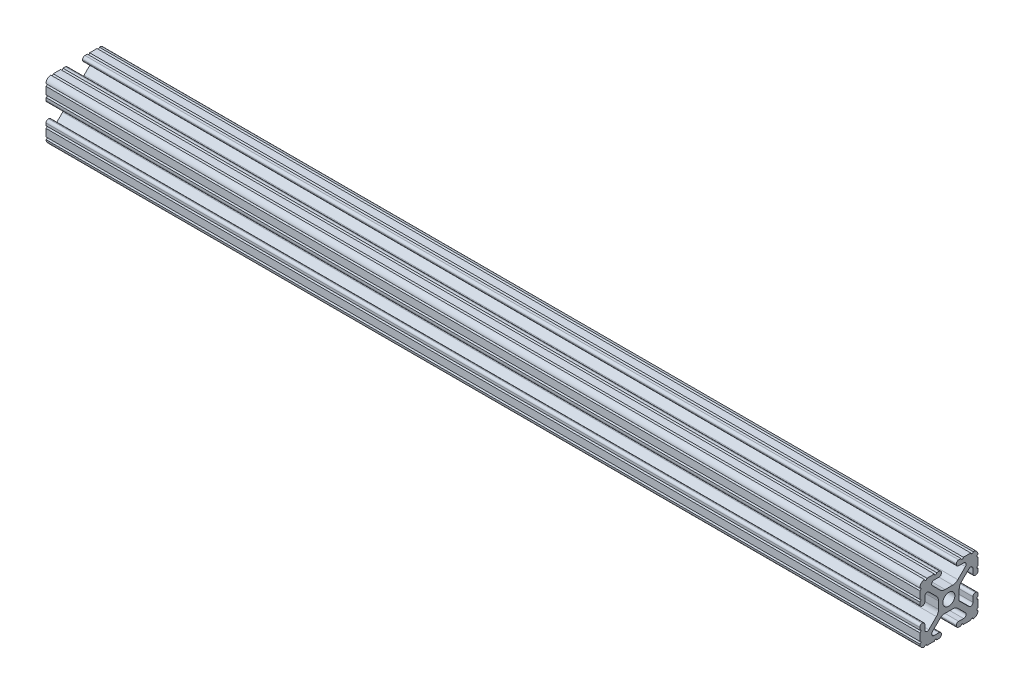
SolidWorks part; units mm, degrees
material "6061-T6 (SS)"
ref_plane "Front Plane" through (0, 0, 0) normal (0, 0, 1) x (1, 0, 0)
ref_plane "Top Plane" through (0, 0, 0) normal (0, 1, 0) x (1, 0, 0)
ref_plane "Right Plane" through (0, 0, 0) normal (1, 0, 0) x (0, 0, -1)
sketch "Sketch1" plane through (0, 0, 0) normal (1, 0, 0) x (0, 0, -1)
  line L0 (6.3331, -12.7) -> (9.5504, -12.7)
  line L1 (12.7, -9.5504) -> (12.7, -6.3331)
  line L2 (12.7, -5.3171) -> (12.7, -4.2875)
  line L3 (11.651, -3.2385) -> (11.5392, -3.2385)
  line L4 (10.4902, -4.2875) -> (10.4902, -6.4021)
  line L5 (8.7371, -7.1294) -> (4.5085, -2.9104)
  line L6 (4.5085, -2.9104) -> (4.5085, 1.5932)
  line L7 (5.441, 3.8408) -> (8.7371, 7.1294)
  line L8 (10.4902, 6.4021) -> (10.4902, 4.2875)
  line L9 (11.5392, 3.2385) -> (11.651, 3.2385)
  line L10 (12.7, 4.2875) -> (12.7, 5.3171)
  line L11 (12.7, 6.3331) -> (12.7, 9.5504)
  line L12 (9.5504, 12.7) -> (6.3331, 12.7)
  line L13 (5.3171, 12.7) -> (4.2875, 12.7)
  line L14 (3.2385, 11.651) -> (3.2385, 11.5392)
  line L15 (4.2875, 10.4902) -> (6.4768, 10.4902)
  line L16 (7.207, 8.7244) -> (3.8983, 5.4232)
  line L17 (1.6558, 4.4958) -> (-1.6558, 4.4958)
  line L18 (-3.8983, 5.4232) -> (-7.207, 8.7244)
  line L19 (-6.4768, 10.4902) -> (-4.2875, 10.4902)
  line L20 (-3.2385, 11.5392) -> (-3.2385, 11.651)
  line L21 (-4.2875, 12.7) -> (-5.3171, 12.7)
  line L22 (-6.3331, 12.7) -> (-9.5504, 12.7)
  line L23 (-12.7, 9.5504) -> (-12.7, 6.3331)
  line L24 (-12.7, 5.3171) -> (-12.7, 4.2875)
  line L25 (-11.651, 3.2385) -> (-11.5392, 3.2385)
  line L26 (-10.4902, 4.2875) -> (-10.4902, 6.4021)
  line L27 (-8.7371, 7.1294) -> (-5.441, 3.8408)
  line L28 (-4.5085, 1.5932) -> (-4.5085, -1.5932)
  line L29 (-5.441, -3.8408) -> (-8.7371, -7.1294)
  line L30 (-10.4902, -6.4021) -> (-10.4902, -4.2875)
  line L31 (-11.5392, -3.2385) -> (-11.651, -3.2385)
  line L32 (-12.7, -4.2875) -> (-12.7, -5.3171)
  line L33 (-12.7, -6.3331) -> (-12.7, -9.5504)
  line L34 (-9.5504, -12.7) -> (-6.3331, -12.7)
  line L35 (-5.3171, -12.7) -> (-4.2875, -12.7)
  line L36 (-3.2385, -11.651) -> (-3.2385, -11.5392)
  line L37 (-4.2875, -10.4902) -> (-6.4164, -10.4902)
  line L38 (-7.1797, -8.6452) -> (-3.9523, -5.4237)
  line L39 (-1.7093, -4.4958) -> (1.7093, -4.4958)
  line L40 (3.9523, -5.4237) -> (7.1797, -8.6452)
  line L41 (6.4164, -10.4902) -> (4.2875, -10.4902)
  line L42 (3.2385, -11.5392) -> (3.2385, -11.651)
  line L43 (4.2875, -12.7) -> (5.3171, -12.7)
  circle A0 centre (0, 0) radius 2.6035
  arc A1 (6.3331, -12.7) -> (5.3171, -12.7) centre (5.8251, -12.7) ccw
  arc A2 (10.5664, -12.6998) -> (9.5504, -12.7) centre (10.0584, -12.7) ccw
  arc A3 (10.5664, -12.6998) -> (12.6998, -10.5664) centre (10.5918, -10.5918) ccw
  arc A4 (12.7, -9.5504) -> (12.6998, -10.5664) centre (12.7, -10.0584) ccw
  arc A5 (12.7, -5.3171) -> (12.7, -6.3331) centre (12.7, -5.8251) ccw
  arc A6 (12.7, -4.2875) -> (11.651, -3.2385) centre (11.651, -4.2875) ccw
  arc A7 (11.5392, -3.2385) -> (10.4902, -4.2875) centre (11.5392, -4.2875) ccw
  arc A8 (8.7371, -7.1294) -> (10.4902, -6.4021) centre (9.4628, -6.4021) ccw
  arc A9 (5.441, 3.8408) -> (4.5085, 1.5932) centre (7.6835, 1.5932) ccw
  arc A10 (10.4902, 6.4021) -> (8.7371, 7.1294) centre (9.4628, 6.4021) ccw
  arc A11 (10.4902, 4.2875) -> (11.5392, 3.2385) centre (11.5392, 4.2875) ccw
  arc A12 (11.651, 3.2385) -> (12.7, 4.2875) centre (11.651, 4.2875) ccw
  arc A13 (12.7, 6.3331) -> (12.7, 5.3171) centre (12.7, 5.8251) ccw
  arc A14 (12.6998, 10.5664) -> (12.7, 9.5504) centre (12.7, 10.0584) ccw
  arc A15 (12.6998, 10.5664) -> (10.5664, 12.6998) centre (10.5918, 10.5918) ccw
  arc A16 (9.5504, 12.7) -> (10.5664, 12.6998) centre (10.0584, 12.7) ccw
  arc A17 (5.3171, 12.7) -> (6.3331, 12.7) centre (5.8251, 12.7) ccw
  arc A18 (4.2875, 12.7) -> (3.2385, 11.651) centre (4.2875, 11.651) ccw
  arc A19 (3.2385, 11.5392) -> (4.2875, 10.4902) centre (4.2875, 11.5392) ccw
  arc A20 (7.207, 8.7244) -> (6.4768, 10.4902) centre (6.4768, 9.4563) ccw
  arc A21 (1.6558, 4.4958) -> (3.8983, 5.4232) centre (1.6558, 7.6708) ccw
  arc A22 (-3.8983, 5.4232) -> (-1.6558, 4.4958) centre (-1.6558, 7.6708) ccw
  arc A23 (-6.4768, 10.4902) -> (-7.207, 8.7244) centre (-6.4768, 9.4563) ccw
  arc A24 (-4.2875, 10.4902) -> (-3.2385, 11.5392) centre (-4.2875, 11.5392) ccw
  arc A25 (-3.2385, 11.651) -> (-4.2875, 12.7) centre (-4.2875, 11.651) ccw
  arc A26 (-6.3331, 12.7) -> (-5.3171, 12.7) centre (-5.8251, 12.7) ccw
  arc A27 (-10.5664, 12.6998) -> (-9.5504, 12.7) centre (-10.0584, 12.7) ccw
  arc A28 (-10.5664, 12.6998) -> (-12.6998, 10.5664) centre (-10.5918, 10.5918) ccw
  arc A29 (-12.7, 9.5504) -> (-12.6998, 10.5664) centre (-12.7, 10.0584) ccw
  arc A30 (-12.7, 5.3171) -> (-12.7, 6.3331) centre (-12.7, 5.8251) ccw
  arc A31 (-12.7, 4.2875) -> (-11.651, 3.2385) centre (-11.651, 4.2875) ccw
  arc A32 (-11.5392, 3.2385) -> (-10.4902, 4.2875) centre (-11.5392, 4.2875) ccw
  arc A33 (-8.7371, 7.1294) -> (-10.4902, 6.4021) centre (-9.4628, 6.4021) ccw
  arc A34 (-4.5085, 1.5932) -> (-5.441, 3.8408) centre (-7.6835, 1.5932) ccw
  arc A35 (-5.441, -3.8408) -> (-4.5085, -1.5932) centre (-7.6835, -1.5932) ccw
  arc A36 (-10.4902, -6.4021) -> (-8.7371, -7.1294) centre (-9.4628, -6.4021) ccw
  arc A37 (-10.4902, -4.2875) -> (-11.5392, -3.2385) centre (-11.5392, -4.2875) ccw
  arc A38 (-11.651, -3.2385) -> (-12.7, -4.2875) centre (-11.651, -4.2875) ccw
  arc A39 (-12.7, -6.3331) -> (-12.7, -5.3171) centre (-12.7, -5.8251) ccw
  arc A40 (-12.6998, -10.5664) -> (-12.7, -9.5504) centre (-12.7, -10.0584) ccw
  arc A41 (-12.6998, -10.5664) -> (-10.5664, -12.6998) centre (-10.5918, -10.5918) ccw
  arc A42 (-9.5504, -12.7) -> (-10.5664, -12.6998) centre (-10.0584, -12.7) ccw
  arc A43 (-5.3171, -12.7) -> (-6.3331, -12.7) centre (-5.8251, -12.7) ccw
  arc A44 (-4.2875, -12.7) -> (-3.2385, -11.651) centre (-4.2875, -11.651) ccw
  arc A45 (-3.2385, -11.5392) -> (-4.2875, -10.4902) centre (-4.2875, -11.5392) ccw
  arc A46 (-7.1797, -8.6452) -> (-6.4164, -10.4902) centre (-6.4164, -9.4098) ccw
  arc A47 (-1.7093, -4.4958) -> (-3.9523, -5.4237) centre (-1.7093, -7.6708) ccw
  arc A48 (3.9523, -5.4237) -> (1.7093, -4.4958) centre (1.7093, -7.6708) ccw
  arc A49 (6.4164, -10.4902) -> (7.1797, -8.6452) centre (6.4164, -9.4098) ccw
  arc A50 (4.2875, -10.4902) -> (3.2385, -11.5392) centre (4.2875, -11.5392) ccw
  arc A51 (3.2385, -11.651) -> (4.2875, -12.7) centre (4.2875, -11.651) ccw
extrude "Boss-Extrude1" add sketch "Sketch1" along normal mid plane 381
